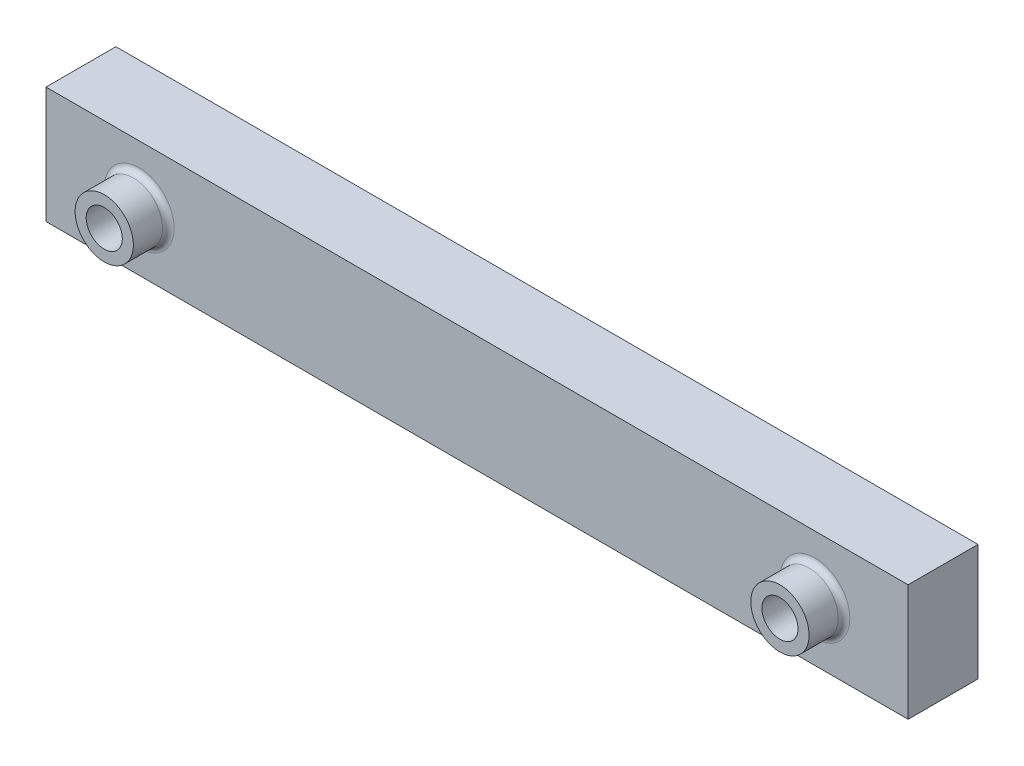
SolidWorks part; units mm, degrees
ref_plane "前视基准面" through (0, 0, 0) normal (0, 0, 1) x (1, 0, 0)
ref_plane "上视基准面" through (0, 0, 0) normal (0, 1, 0) x (1, 0, 0)
ref_plane "右视基准面" through (0, 0, 0) normal (1, 0, 0) x (0, 0, -1)
sketch "草图1" plane through (0, 0, 0) normal (0, 0, 1) x (1, 0, 0)
  line L1 (-24.0996, 6.3351) -> (49.9004, 6.3351)
  line L2 (-24.0996, 6.3351) -> (-24.0996, -3.6649)
  line L3 (-24.0996, -3.6649) -> (49.9004, -3.6649)
  line L4 (49.9004, 6.3351) -> (49.9004, -3.6649)
  dimension "D1" = 74
  dimension "D2" = 10
extrude "凸台-拉伸1" add sketch "草图1" along normal blind 6
sketch "草图2" plane through (0, 0, 6) normal (0, 0, 1) x (1, 0, 0)
  line L0 (-24.0996, 1.3351) -> (55.6004, 1.3351) construction
  line L1 (-24.0996, 6.3351) -> (-24.0996, -3.6649) construction
  line L2 (12.9004, -8.7036) -> (12.9004, 14.3252) construction
  circle A0 centre (-16.0996, 1.3351) radius 1.55
  circle A1 centre (41.9004, 1.3351) radius 1.55
  dimension "D4" = 3.1
  dimension "D5" = 3.1
  dimension "D1" = 29
  dimension "D2" = 29
  dimension "D3" = 37
extrude "切除-拉伸1" cut sketch "草图2" against normal blind 10
sketch "草图3" plane through (0, 0, 6) normal (0, 0, 1) x (1, 0, 0)
  circle A0 centre (-16.0996, 1.3351) radius 2.5
  circle A1 centre (41.9004, 1.3351) radius 2.5
  circle A2 centre (-16.0996, 1.3351) radius 1.55
  circle A3 centre (41.9004, 1.3351) radius 1.55
  dimension "D1" = 5
  dimension "D2" = 5
extrude "凸台-拉伸2" add sketch "草图3" along normal blind 3
fillet "圆角5" radius 0.5 1 edges at (44.4004, 1.3351, 6)
fillet "圆角7" radius 0.5 1 edges at (-13.5996, 1.3351, 6)
